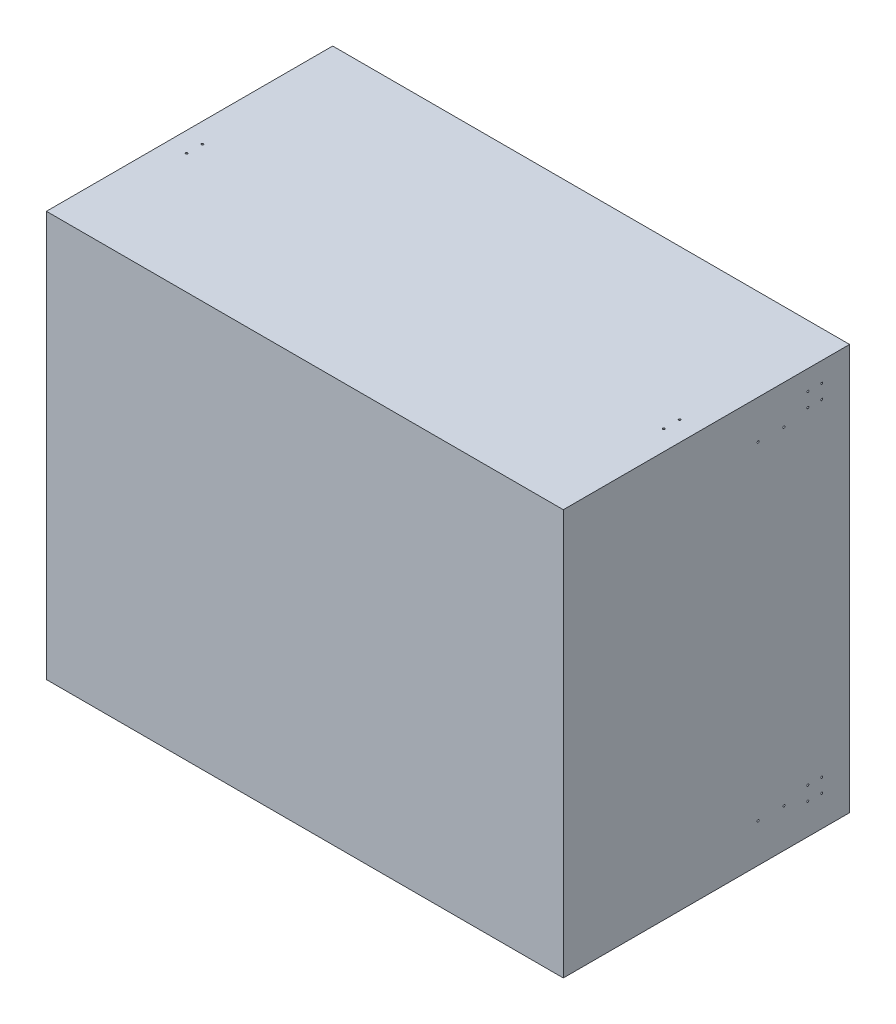
SolidWorks part; units mm, degrees
material "Custom Plastic"
ref_plane "Front Plane" through (0, 0, 0) normal (0, 0, 1) x (1, 0, 0)
ref_plane "Top Plane" through (0, 0, 0) normal (0, 1, 0) x (1, 0, 0)
ref_plane "Right Plane" through (0, 0, 0) normal (1, 0, 0) x (0, 0, -1)
sketch "Sketch1" plane through (0, 0, 0) normal (0, 0, 1) x (1, 0, 0)
  line L0 (-650, 510) -> (-650, -510)
  line L1 (-650, -510) -> (650, -510)
  line L2 (650, -510) -> (650, 510)
  line L3 (650, 510) -> (-650, 510)
  line L4 (0, 966.6667) -> (0, -1043.3333) construction
  line L5 (-1916.6667, 0) -> (1420, 0) construction
  point P7 (0, 510)
  point P10 (-650, 0)
  dimension "D1" = 1020
  dimension "D2" = 1300
extrude "Boss-Extrude2" add sketch "Sketch1" along normal blind 720
sketch "Sketch3" plane through (0, 0, 0) normal (0, 0, 1) x (1, 0, 0)
  line L0 (650, -510) -> (650, 510) construction
  line L1 (640, 500) -> (-640, 500)
  line L2 (640, 500) -> (640, -500)
  line L3 (640, -500) -> (-640, -500)
  line L4 (-640, 500) -> (-640, -500)
  line L5 (640, 500) -> (-640, -500) construction
  line L6 (640, -500) -> (-640, 500) construction
  line L7 (650, 510) -> (-650, 510) construction
  point P0 (0, 0)
  dimension "D1" = 10
  dimension "D2" = 10
extrude "Cut-Extrude1" cut sketch "Sketch3" along normal blind 710
sketch "Sketch4" plane through (0, 0, 0) normal (1, 0, 0) x (0, 0, -1)
  line L0 (-90, 553.3793) -> (-90, -579.3596) construction
  line L1 (0, -510) -> (0, 510) construction
  line L2 (-70, 553.3793) -> (-70, -529.9971) construction
  line L3 (-105, 553.3793) -> (-105, -529.9971) construction
  line L4 (-1075.2665, 460) -> (170.4865, 460) construction
  line L5 (-1075.2665, -432.5) -> (135.4131, -432.5) construction
  line L6 (-720, 510) -> (0, 510) construction
  line L7 (-720, -510) -> (0, -510) construction
  line L8 (-1075.2665, 425) -> (170.4865, 425) construction
  line L9 (-1075.2665, -397.5) -> (135.4131, -397.5) construction
  circle A0 centre (-70, 460) radius 2.5
  circle A1 centre (-105, 460) radius 2.5
  circle A2 centre (-105, 425) radius 2.5
  circle A3 centre (-70, 425) radius 2.5
  circle A4 centre (-105, -432.5) radius 2.5
  circle A5 centre (-105, -397.5) radius 2.5
  circle A6 centre (-70, -397.5) radius 2.5
  circle A7 centre (-70, -432.5) radius 2.5
  dimension "D6" = 5
  dimension "D7" = 5
  dimension "D10" = 5
  dimension "D11" = 5
  dimension "D12" = 5
  dimension "D13" = 5
  dimension "D14" = 5
  dimension "D15" = 5
  dimension "D1" = 90
  dimension "D2" = 15
  dimension "D3" = 20
  dimension "D4" = 50
  dimension "D5" = 77.5
  dimension "D8" = 35
  dimension "D9" = 35
extrude "Cut-Extrude2" cut sketch "Sketch4" against normal through all both and the other way through all
sketch "Sketch6" plane through (650, 0, 0) normal (1, 0, 0) x (0, 0, -1)
  line L0 (-720, 510) -> (0, 510) construction
  line L1 (-720, -510) -> (0, -510) construction
  line L2 (0, -510) -> (0, 510) construction
  circle A0 centre (-105, 460) radius 2.5
  circle A1 centre (-230, 412.5) radius 2.5
  circle A2 centre (-165, 412.5) radius 2.5
  circle A4 centre (-165, -412.5) radius 2.5
  circle A6 centre (-230, -412.5) radius 2.5
  dimension "D1" = 5
  dimension "D2" = 5
  dimension "D5" = 5
  dimension "D6" = 5
  dimension "D3" = 97.5
  dimension "D4" = 97.5
  dimension "D7" = 97.5
  dimension "D8" = 97.5
  dimension "D9" = 65
  dimension "D10" = 65
  dimension "D11" = 165
  dimension "D12" = 165
extrude "Cut-Extrude5" cut sketch "Sketch6" against normal blind 3326.5
sketch "Sketch7" plane through (0, 0, 0) normal (0, 1, 0) x (1, 0, 0)
  line L0 (650, 0) -> (-650, 0) construction
  line L1 (650, -720) -> (650, 0) construction
  line L2 (0, 293.8095) -> (0, -1181.1513) construction
  circle A0 centre (600, -417.5) radius 2.5
  circle A1 centre (600, -377.5) radius 2.5
  circle A2 centre (-600, -417.5) radius 2.5
  circle A3 centre (-600, -377.5) radius 2.5
  dimension "D3" = 5
  dimension "D4" = 5
  dimension "D1" = 377.5
  dimension "D2" = 417.5
  dimension "D5" = 50
  dimension "D6" = 50
extrude "Cut-Extrude6" cut sketch "Sketch7" against normal blind 886 and the other way blind 652
